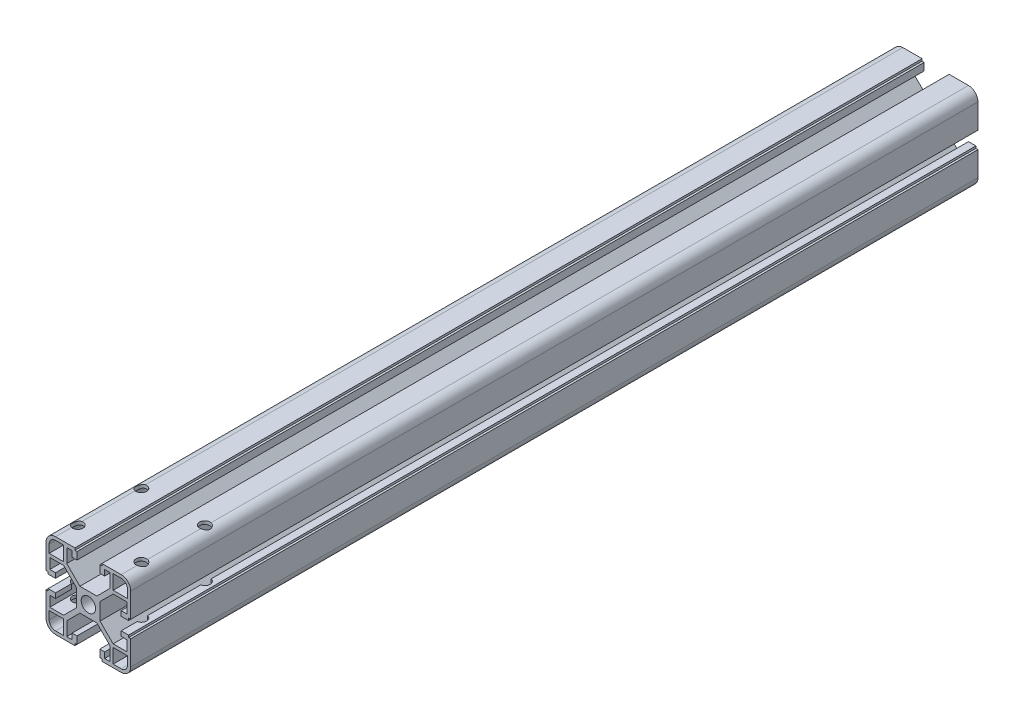
SolidWorks part; units mm, degrees
material "6061-T6 (SS)"
ref_plane "Front Plane" through (0, 0, 0) normal (0, 0, 1) x (1, 0, 0)
ref_plane "Top Plane" through (0, 0, 0) normal (0, 1, 0) x (1, 0, 0)
ref_plane "Right Plane" through (0, 0, 0) normal (1, 0, 0) x (0, 0, -1)
sketch "Sketch1" plane through (0, 0, 0) normal (0, 0, 1) x (1, 0, 0)
  line L0 (3.4, 0) -> (5.5, 0)
  line L1 (10.19, 11.69) -> (4, 5.5)
  line L2 (11.69, 10.19) -> (5.5, 4)
  line L3 (18.2, 10.19) -> (11.69, 10.19)
  line L4 (18.2, 10.19) -> (18.2, 5.2656)
  line L5 (18.2, 5.2656) -> (15.5, 5.2656)
  line L6 (15.5, 5.2656) -> (15.5, 2.9656)
  line L7 (15.5, 2.9656) -> (19, 2.9656)
  line L8 (19, 2.9656) -> (19, 3.9656)
  line L9 (19, 3.9656) -> (20, 3.9656)
  line L10 (20, 3.9656) -> (20, 15.5)
  line L11 (15.5, 20) -> (6.3853, 20)
  line L12 (18.5, 11.69) -> (18.5, 15.5)
  line L13 (15.5, 18.5) -> (11.69, 18.5)
  line L14 (11.69, 11.69) -> (11.69, 18.5)
  line L15 (0, 3.4) -> (0, 5.5)
  line L16 (4, 5.5) -> (0, 5.5)
  line L17 (6.3853, 20) -> (6.3853, 19)
  line L18 (5.5, 0) -> (5.5, 4)
  line L19 (6.3853, 19) -> (5.3853, 19)
  line L20 (5.3853, 19) -> (5.3853, 15.5)
  line L21 (5.3853, 15.5) -> (7.6853, 15.5)
  line L22 (10.19, 11.69) -> (10.19, 18.2)
  line L23 (11.69, 11.69) -> (18.5, 11.69)
  line L24 (7.6853, 18.2) -> (7.6853, 15.5)
  line L25 (10.19, 18.2) -> (7.6853, 18.2)
  arc A0 (20, 15.5) -> (15.5, 20) centre (15.5, 15.5) ccw
  arc A1 (18.5, 15.5) -> (15.5, 18.5) centre (15.5, 15.5) ccw
  arc A2 (3.4, 0) -> (0, 3.4) centre (0, 0) ccw
  dimension "D3" = 4.5
  dimension "D18" = 1.5
  dimension "D9" = 3.4
  dimension "D20" = 1.8
  dimension "D25" = 3
  dimension "D1" = 5.5
  dimension "D2" = 1.5
  dimension "D4" = 14.5
  dimension "D5" = 1.5
  dimension "D6" = 2.1
  dimension "D7" = 2.3
  dimension "D8" = 1.8
  dimension "D10" = 6.81
  dimension "D11" = 2.1
  dimension "D12" = 1
  dimension "D13" = 4.5
  dimension "D14" = 45
  dimension "D15" = 14.5
  dimension "D16" = 1
  dimension "D17" = 1.5
  dimension "D19" = 6.81
  dimension "D21" = 4.5
  dimension "D22" = 2.3
  dimension "D23" = 1
  dimension "D24" = 1
  dimension "D26" = 8.754
  dimension "D27" = 8.754
  dimension "D28" = 4.9244
  dimension "D29" = 2.5047
extrude "Boss-Extrude1" add sketch "Sketch1" along normal blind 400
mirror "Mirror1" about plane through (0, 0, 0) normal (0, 1, 0) of "Boss-Extrude1"
mirror "Mirror2" about plane through (0, 0, 0) normal (1, 0, 0) of "Boss-Extrude1"
mirror "Mirror3" about plane through (0, 0, 0) normal (0, 1, 0) of "Mirror2"
sketch "Sketch2" plane through (0, 5.5, 0) normal (0, 1, 0) x (1, 0, 0)
  line L0 (4, 0) -> (-4, 0) construction
  line L2 (-15, -360) -> (15, -360) construction
  line L3 (-15, -360) -> (-15, -390) construction
  line L4 (-15, -390) -> (15, -390) construction
  line L5 (15, -360) -> (15, -390) construction
  line L6 (-15, -360) -> (15, -390) construction
  line L7 (-15, -390) -> (15, -360) construction
  line L8 (4, -400) -> (-4, -400) construction
  circle A0 centre (0, -10) radius 2.5
  circle A1 centre (0, -60) radius 2.5
  circle A2 centre (-15, -360) radius 2.5
  circle A3 centre (15, -360) radius 2.5
  circle A4 centre (15, -390) radius 2.5
  circle A5 centre (-15, -390) radius 2.5
  point P7 (0, -375)
  dimension "D1" = 50
  dimension "D2" = 10
  dimension "D3" = 5
  dimension "D7" = 5
  dimension "D4" = 30
  dimension "D5" = 30
  dimension "D6" = 10
extrude "Cut-Extrude1" cut sketch "Sketch2" against normal through all both and the other way through all
